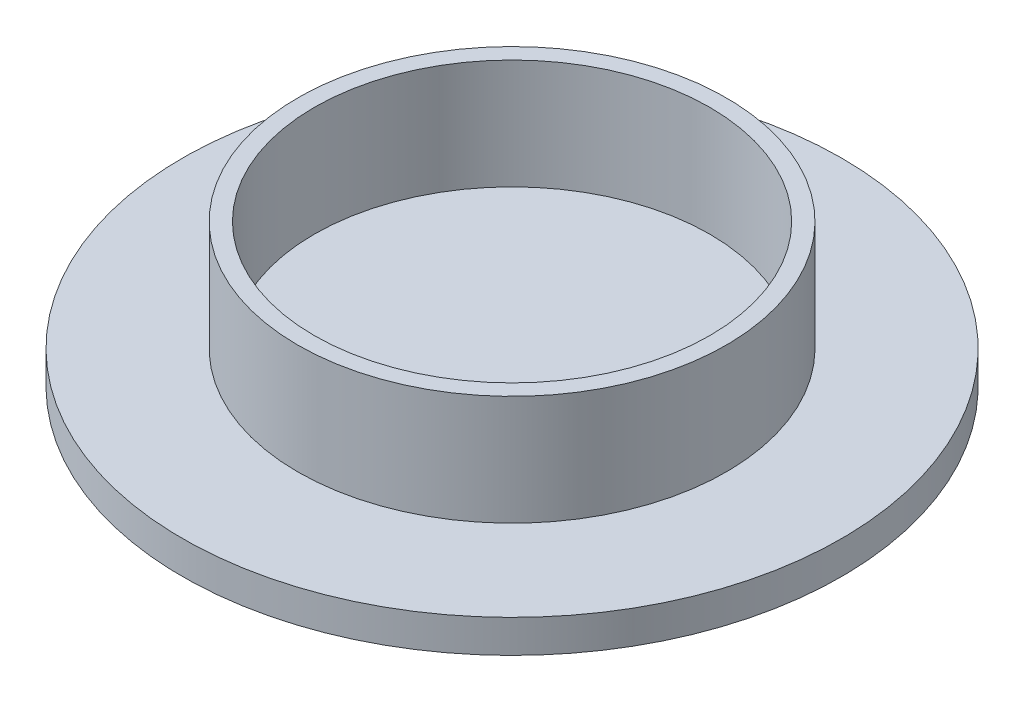
SolidWorks part; units mm, degrees
ref_plane "前基準面" through (0, 0, 0) normal (0, 0, 1) x (1, 0, 0)
ref_plane "上基準面" through (0, 0, 0) normal (0, 1, 0) x (1, 0, 0)
ref_plane "右基準面" through (0, 0, 0) normal (1, 0, 0) x (0, 0, -1)
sketch "草圖1" plane through (0, 0, 0) normal (0, 1, 0) x (1, 0, 0)
  circle A0 centre (0, 0) radius 19.5
  circle A1 centre (0, 0) radius 18
  dimension "D1" = 39
  dimension "D2" = 36
extrude "填料-伸長1" add sketch "草圖1" along normal blind 10
sketch "草圖3" plane through (0, 0, 0) normal (0, -1, 0) x (1, 0, 0)
  circle A0 centre (0, 0) radius 30
  dimension "D1" = 60
extrude "填料-伸長2" add sketch "草圖3" along normal blind 3
